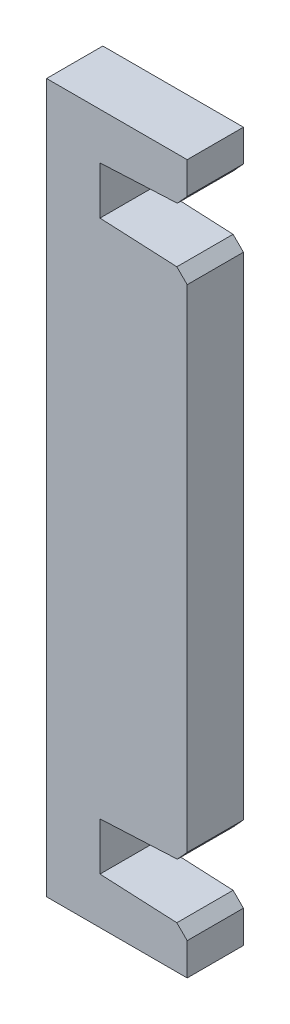
SolidWorks part; units mm, degrees
material "Oak"
ref_plane "Front Plane" through (0, 0, 0) normal (0, 0, 1) x (1, 0, 0)
ref_plane "Top Plane" through (0, 0, 0) normal (0, 1, 0) x (1, 0, 0)
ref_plane "Right Plane" through (0, 0, 0) normal (1, 0, 0) x (0, 0, -1)
sketch "Sketch1" plane through (0, 0, 0) normal (0, 0, 1) x (1, 0, 0)
  line L0 (0, -18.2) -> (0, 18.2)
  line L1 (0, 18.2) -> (-6.2, 18.5)
  line L2 (-6.2, 18.5) -> (-6.2, 21.9)
  line L3 (-6.2, 21.9) -> (0, 22.2)
  line L4 (0, 22.2) -> (0, 25.2)
  line L5 (0, 25.2) -> (-10, 25.2)
  line L6 (-10, 25.2) -> (-10, -25.2)
  line L7 (-10, 0) -> (0, 0)
  line L8 (-20.8617, 0) -> (22.0865, 0) construction
  line L9 (0, -25.2) -> (-10, -25.2)
  line L10 (0, -22.2) -> (0, -25.2)
  line L11 (-6.2, -21.9) -> (0, -22.2)
  line L12 (-6.2, -18.5) -> (-6.2, -21.9)
  line L13 (0, -18.2) -> (-6.2, -18.5)
  dimension "D1" = 4
  dimension "D2" = 3.4
  dimension "D3" = 37
  dimension "D4" = 3.8
  dimension "D5" = 10
  dimension "D6" = 3
extrude "Boss-Extrude1" add sketch "Sketch1" along normal blind 4 contours L6 L7 L0 L1 L2 L3 L4 L5 | L13 L0 L7 L6 L9 L10 L11 L12
chamfer "Chamfer1" distance 0.7 angle 45 4 edges at (0, -18.2, 2) (0, -22.2, 2) (0, 18.2, 2) (0, 22.2, 2)
